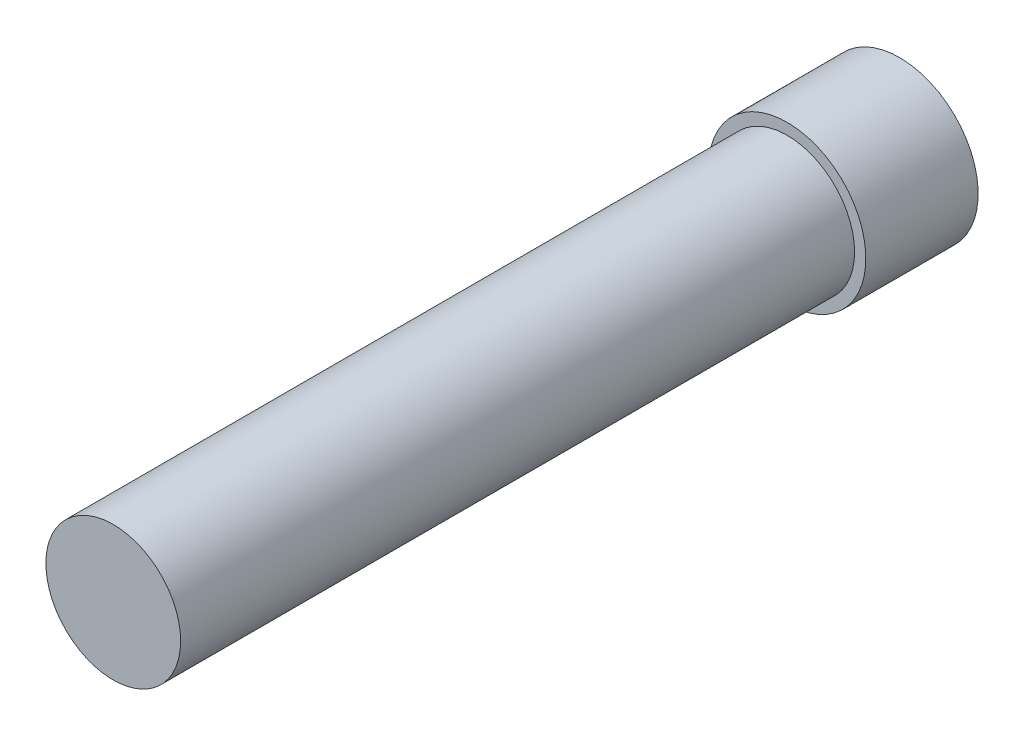
SolidWorks part; units mm, degrees
ref_plane "Front Plane" through (0, 0, 0) normal (0, 0, 1) x (1, 0, 0)
ref_plane "Top Plane" through (0, 0, 0) normal (0, 1, 0) x (1, 0, 0)
ref_plane "Right Plane" through (0, 0, 0) normal (1, 0, 0) x (0, 0, -1)
sketch "Sketch1" plane through (0, 0, 0) normal (0, 0, 1) x (1, 0, 0)
  circle A0 centre (0, 0) radius 3
  dimension "D1" = 6
extrude "Boss-Extrude1" add sketch "Sketch1" along normal blind 30
sketch "Sketch2" plane through (0, 0, 0) normal (0, 0, -1) x (-1, 0, 0)
  circle A0 centre (0, 0) radius 3.5
  dimension "D1" = 7
extrude "Boss-Extrude2" add sketch "Sketch2" along normal blind 5
